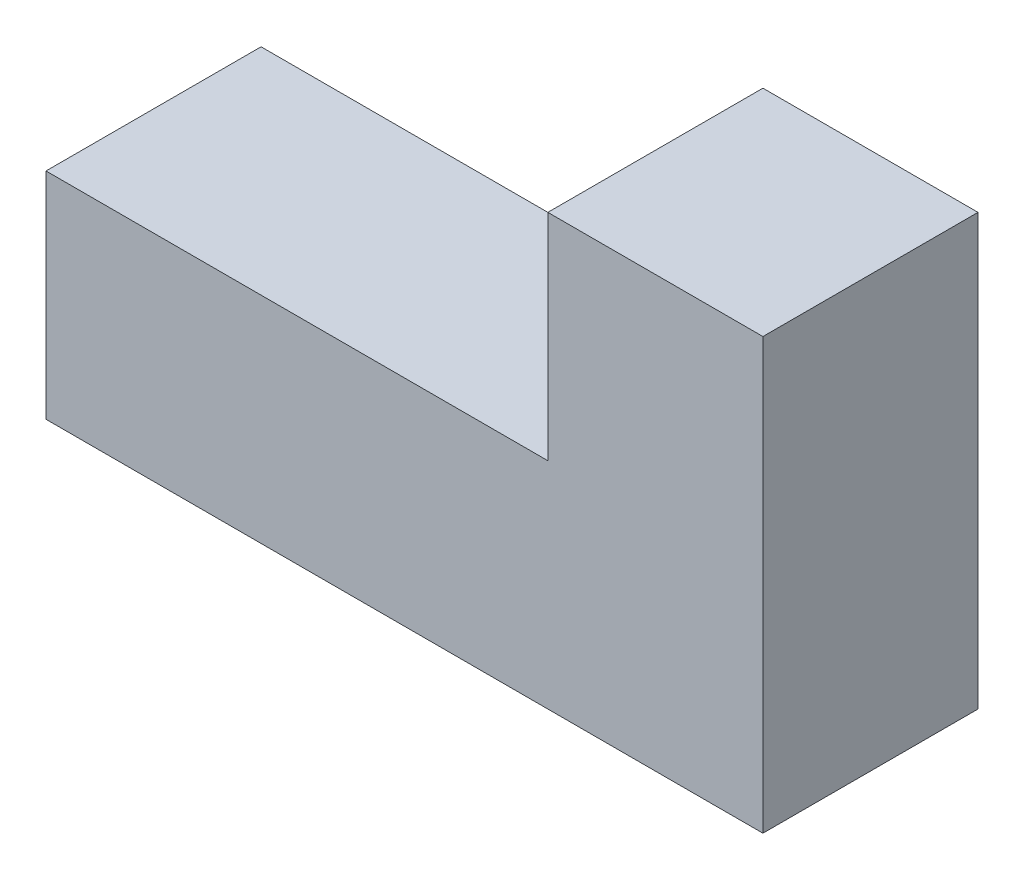
SolidWorks part; units mm, degrees
ref_plane "Спереди" through (0, 0, 0) normal (0, 0, 1) x (1, 0, 0)
ref_plane "Сверху" through (0, 0, 0) normal (0, 1, 0) x (1, 0, 0)
ref_plane "Справа" through (0, 0, 0) normal (1, 0, 0) x (0, 0, -1)
sketch "Эскиз1" plane through (0, 0, 0) normal (0, 0, 1) x (1, 0, 0)
  line L0 (0, 0) -> (100, 0)
  line L1 (100, 0) -> (100, 60)
  line L2 (0, 0) -> (0, 30)
  line L3 (0, 30) -> (70, 30)
  line L4 (70, 30) -> (70, 60)
  line L5 (70, 60) -> (100, 60)
extrude "Бобышка-Вытянуть1" add sketch "Эскиз1" along normal blind 30
